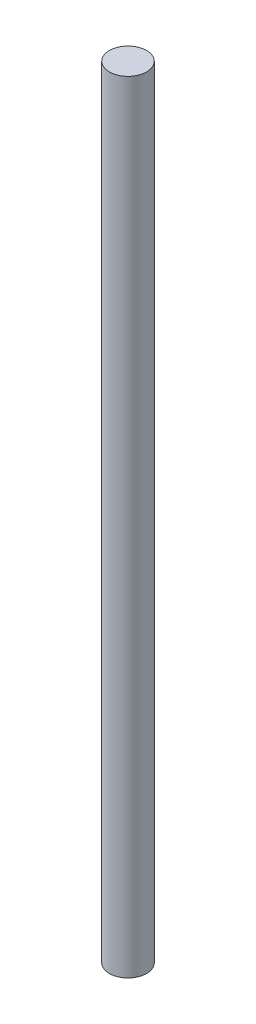
SolidWorks part; units mm, degrees
ref_plane "Front" through (0, 0, 0) normal (0, 0, 1) x (1, 0, 0)
ref_plane "Top" through (0, 0, 0) normal (0, 1, 0) x (1, 0, 0)
ref_plane "Right" through (0, 0, 0) normal (1, 0, 0) x (0, 0, -1)
sketch "Sketch1" plane through (0, 0, 0) normal (0, 1, 0) x (1, 0, 0)
  circle A0 centre (0, 0) radius 1.5
  dimension "D1" = 3
extrude "Boss-Extrude1" add sketch "Sketch1" along normal blind 63
